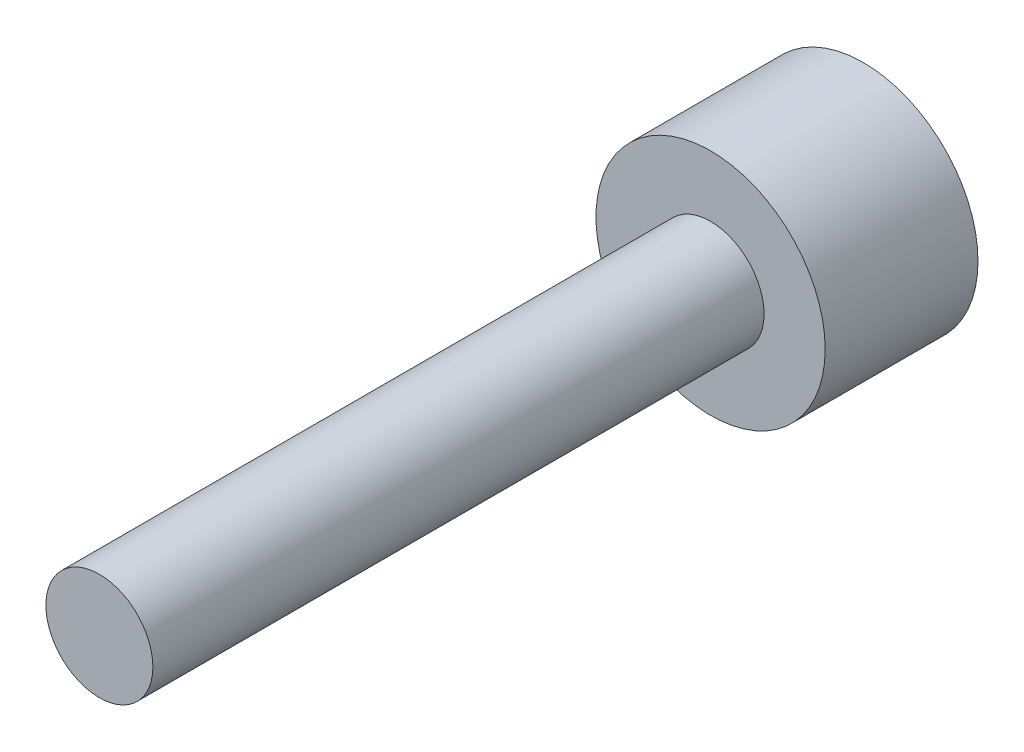
SolidWorks part; units mm, degrees
ref_plane "前基準面" through (0, 0, 0) normal (0, 0, 1) x (1, 0, 0)
ref_plane "上基準面" through (0, 0, 0) normal (0, 1, 0) x (1, 0, 0)
ref_plane "右基準面" through (0, 0, 0) normal (1, 0, 0) x (0, 0, -1)
sketch "草圖1" plane through (0, 0, 0) normal (0, 0, 1) x (1, 0, 0)
  circle A0 centre (0, 0) radius 0.7
  dimension "D1" = 1.4
extrude "填料-伸長1" add sketch "草圖1" along normal blind 10
sketch "草圖2" plane through (0, 0, 0) normal (0, 0, 1) x (1, 0, 0)
  circle A0 centre (0, 0) radius 1.5
  dimension "D1" = 3
extrude "填料-伸長2" add sketch "草圖2" along normal blind 2
